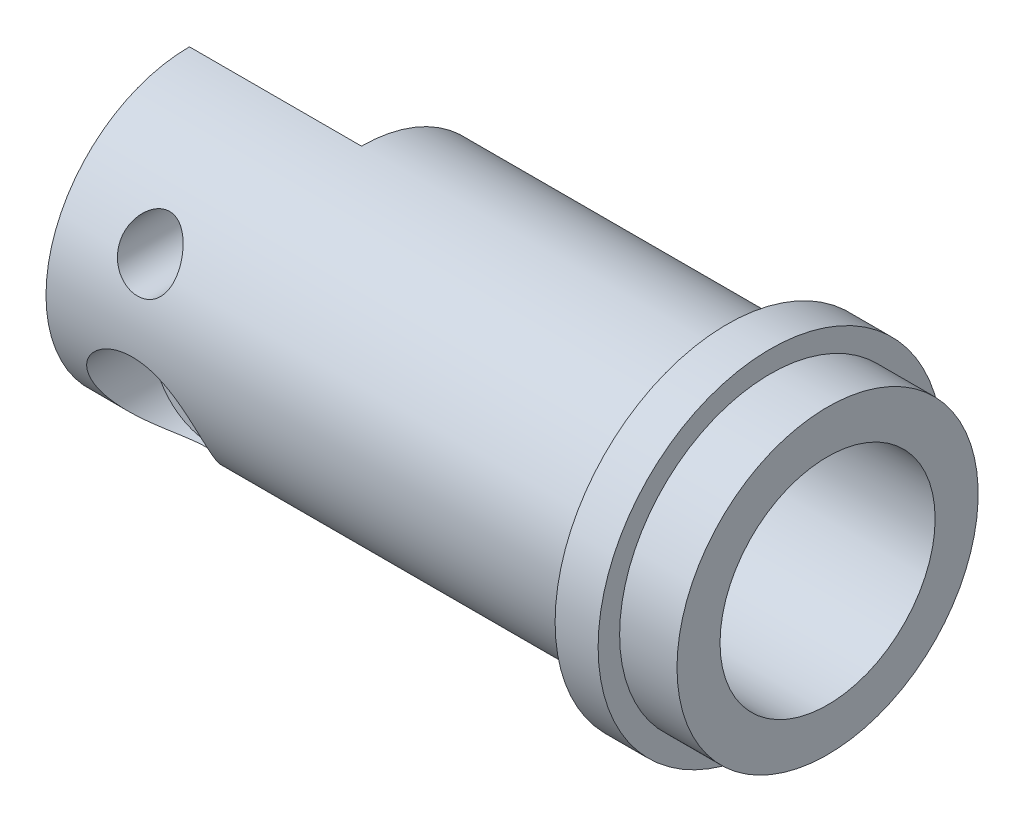
SolidWorks part; units mm, degrees
material "1.0037 (S235JR)"
ref_plane "Płaszczyzna XY" through (0, 0, 0) normal (0, 0, 1) x (1, 0, 0)
ref_plane "Płaszczyzna XZ" through (0, 0, 0) normal (0, 1, 0) x (1, 0, 0)
ref_plane "Płaszczyzna YZ" through (0, 0, 0) normal (1, 0, 0) x (0, 0, -1)
sketch "Szkic1" plane through (0, 0, 0) normal (0, 1, 0) x (1, 0, 0)
  line L0 (28.2857, 0) -> (40.7857, 0)
  line L1 (60.7857, 7.5) -> (60.7857, 10.5)
  line L2 (60.7857, 10.5) -> (56.7857, 10.5)
  line L3 (56.7857, 10.5) -> (56.7857, 12)
  line L4 (56.7857, 12) -> (53.7857, 12)
  line L5 (53.7857, 12) -> (53.7857, 10)
  line L6 (53.7857, 10) -> (28.2857, 10)
  line L10 (60.7857, 7.5) -> (40.7857, 7.5)
  line L11 (40.7857, 7.5) -> (40.7857, 0)
  line L14 (28.2857, 10) -> (28.2857, 0)
  point P0 (28.2857, 10)
  dimension "D1" = 25.5
  dimension "D3" = 10
  dimension "D4" = 2
  dimension "D5" = 3
  dimension "D6" = 4
  dimension "D7" = 7.5
  dimension "D8" = 20
revolve "Obrót1" add sketch "Szkic1" angle 360 about L0
sketch "Szkic2" plane through (28.2857, 0, 0) normal (-1, 0, 0) x (0, 0, 1)
  line L0 (0, -10) -> (0, 10)
  circle A0 centre (0, 0) radius 10 construction
  circle A1 centre (0, 0) radius 10 construction
  arc A2 (0, -10) -> (0, 10) centre (0, 0) ccw
extrude "Dodanie-wyciągnięcie1" add sketch "Szkic2" along normal blind 12
chamfer "Sfazowanie1" [suppressed] distance 0.5 angle 45
sketch "Szkic3" plane through (0, 0, 0) normal (0, 0, 1) x (1, 0, 0)
  line L0 (22.2857, -10) -> (22.2857, 10)
  line L1 (16.2857, -10) -> (28.2857, -10) construction
  line L2 (16.2857, 10) -> (28.2857, 10) construction
  line L3 (16.2857, 0) -> (28.2857, -9.5)
  line L4 (16.2857, 10) -> (16.2857, -10) construction
  line L5 (16.2857, 0) -> (28.2857, 9.5)
  line L6 (28.2857, 10) -> (28.2857, -10) construction
  line L7 (53.7857, 10) -> (28.2857, 10) construction
  circle A0 centre (22.2857, 4.75) radius 2
  circle A1 centre (22.2857, -4.75) radius 2
  point P10 (28.2857, 9.5)
  point P17 (28.2857, -9.5)
  dimension "D1" = 4
  dimension "D2" = 4
  dimension "D3" = 0.5
  dimension "D4" = 0.5
extrude "Wytnij-wyciągnięcie1" cut sketch "Szkic3" along normal blind 12 contours A0 | A1
sketch "Szkic5" plane through (0, 0, 0) normal (0, 1, 0) x (1, 0, 0)
  line L0 (22.2857, 0) -> (22.2857, -7.3782)
  line L1 (16.2857, 0) -> (28.2857, 0) construction
  line L2 (24.2982, -7.3782) -> (20.2919, -7.3782)
  spline S0 degree 3 poles (20.2857, -8.6647) (20.2857, -8.935) (20.3334, -9.0589) (20.48, -9.2174) (20.5421, -9.2665) (20.6902, -9.3545) (20.7755, -9.3933) (21.067, -9.4963) (21.3052, -9.5449) (21.6999, -9.5906) (21.8354, -9.6011) (22.1142, -9.6138) (22.2577, -9.6158) (22.6789, -9.609) (22.9581, -9.5874) (23.3295, -9.5275) (23.4478, -9.5024) (23.6604, -9.4435) (23.7562, -9.4094) (23.9271, -9.3305) (24.0008, -9.286) (24.1217, -9.1894) (24.1698, -9.1368) (24.2421, -9.0221) (24.2657, -8.9607) (24.2887, -8.8334) (24.2885, -8.767) (24.2659, -8.6284) (24.2431, -8.5561) (24.1776, -8.4114) (24.1347, -8.3383) (24.0289, -8.1912) (23.9656, -8.1169) (23.8218, -7.9735) (23.7411, -7.9036) (23.5599, -7.7695) (23.4588, -7.7051) (23.2414, -7.5899) (23.1245, -7.5386) (22.8701, -7.453) (22.7375, -7.4206) (22.46, -7.3807) (22.3176, -7.3739) (22.0373, -7.3878) (21.8962, -7.4089) (21.6315, -7.4731) (21.5046, -7.5167) (21.2687, -7.6192) (21.1608, -7.6773) (20.9616, -7.8036) (20.87, -7.8721) (20.7082, -8.0117) (20.637, -8.0835) (20.5125, -8.2293) (20.4591, -8.304) (20.331, -8.5234) (20.2857, -8.6647) (20.2857, -8.935) (20.3334, -9.0589) knots -0.0625 -0.0625 0 0 0.0625 0.0625 0.09375 0.09375 0.125 0.125 0.1875 0.1875 0.21875 0.21875 0.25 0.25 0.3125 0.3125 0.34375 0.34375 0.375 0.375 0.40625 0.40625 0.4375 0.4375 0.46875 0.46875 0.5 0.5 0.53125 0.53125 0.5625 0.5625 0.59375 0.59375 0.625 0.625 0.65625 0.65625 0.6875 0.6875 0.71875 0.71875 0.75 0.75 0.78125 0.78125 0.8125 0.8125 0.84375 0.84375 0.875 0.875 0.90625 0.90625 0.9375 0.9375 1 1 1.0625 1.0625 1.09375 only from (20.2857, -8.7999) to (20.2857, -8.7999) construction
  point P7 (22.2857, -4.5)
  dimension "D1" = 4.5
ref_plane "Płaszczyzna1" through (0, 0, 4.5) normal (0, 0, -1) x (-1, 0, 0)
sketch "Szkic6" plane through (0, 0, 4.5) normal (0, 0, -1) x (-1, 0, 0)
  circle A0 centre (-22.2857, -4.75) radius 4
  dimension "D1" = 8
extrude "Wytnij-wyciągnięcie2" cut sketch "Szkic6" against normal blind 12 contours A0
sketch "Szkic7" plane through (40.7857, 0, 0) normal (1, 0, 0) x (0, 0, -1)
  circle A0 centre (0, 0) radius 3
  dimension "D1" = 6
extrude "Wytnij-wyciągnięcie3" cut sketch "Szkic7" against normal blind 14.5 contours A0
sketch "Szkic9" plane through (0, 0, 0) normal (0, 0, 1) x (1, 0, 0)
  line L0 (28.2857, 3) -> (28.2857, -3) construction
  circle A0 centre (28.2857, 0) radius 2.5
extrude "Wytnij-wyciągnięcie5" cut sketch "Szkic9" against normal through all
sketch "Szkic8" plane through (0, 0, 0) normal (0, 1, 0) x (1, 0, 0)
  circle A1 centre (28.2857, 0) radius 2
